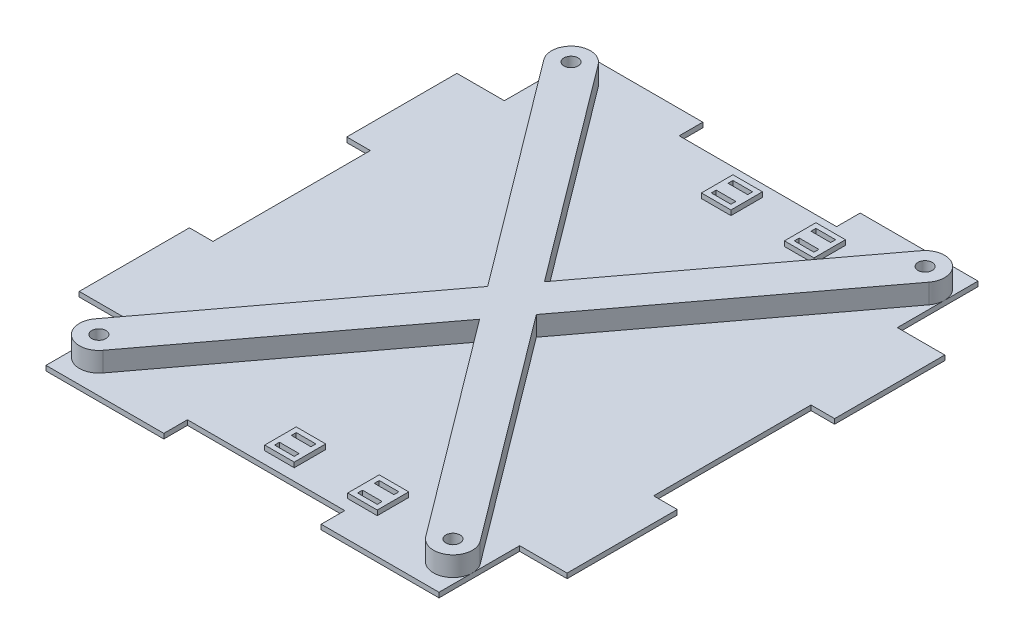
SolidWorks part; units mm, degrees
ref_plane "Front Plane" through (0, 0, 0) normal (0, 0, 1) x (1, 0, 0)
ref_plane "Top Plane" through (0, 0, 0) normal (0, 1, 0) x (1, 0, 0)
ref_plane "Right Plane" through (0, 0, 0) normal (1, 0, 0) x (0, 0, -1)
sketch "Sketch1" plane through (0, 0, 0) normal (0, 1, 0) x (1, 0, 0)
  line L0 (-25.4, 86.995) -> (-63.4314, 86.995)
  line L1 (-88.9, -101.6) -> (88.9, -101.6) construction
  line L2 (101.6, -88.9) -> (101.6, 88.9) construction
  line L3 (88.9, 101.6) -> (-88.9, 101.6) construction
  line L4 (-78.74, -60.96) -> (-63.4314, -60.96)
  line L5 (-63.4314, -60.96) -> (-63.4314, -86.995)
  line L6 (-63.4314, -86.995) -> (-25.4, -86.995)
  line L7 (63.4314, -86.995) -> (63.4314, -60.96)
  line L8 (63.4314, -60.96) -> (78.74, -60.96)
  line L9 (78.74, -60.96) -> (78.74, -25.4)
  line L10 (78.74, 60.96) -> (63.4314, 60.96)
  line L11 (63.4314, 60.96) -> (63.4314, 86.995)
  line L12 (63.4314, 86.995) -> (25.4, 86.995)
  line L13 (-63.4314, 86.995) -> (-63.4314, 60.96)
  line L14 (-63.4314, 60.96) -> (-78.74, 60.96)
  line L15 (-78.74, 60.96) -> (-78.74, 25.4)
  line L16 (-78.74, -25.4) -> (-78.74, -60.96)
  line L17 (-78.74, -25.4) -> (-71.12, -25.4)
  line L19 (-78.74, 25.4) -> (-71.12, 25.4)
  line L20 (-71.12, -25.4) -> (-71.12, 25.4)
  line L22 (-25.4, 86.995) -> (-25.4, 79.375)
  line L23 (-25.4, 79.375) -> (25.4, 79.375)
  line L24 (25.4, 86.995) -> (25.4, 79.375)
  line L25 (78.74, 25.4) -> (71.12, 25.4)
  line L27 (78.74, -25.4) -> (71.12, -25.4)
  line L28 (71.12, 25.4) -> (71.12, -25.4)
  line L30 (25.4, -86.995) -> (25.4, -79.375)
  line L31 (25.4, -79.375) -> (-25.4, -79.375)
  line L32 (-25.4, -86.995) -> (-25.4, -79.375)
  line L33 (78.74, 25.4) -> (78.74, 60.96)
  line L34 (25.4, -86.995) -> (63.4314, -86.995)
  line L35 (-101.6, 88.9) -> (-101.6, -88.9) construction
  arc A0 (88.9, -101.6) -> (101.6, -88.9) centre (88.9, -88.9) ccw construction
  arc A1 (-101.6, -88.9) -> (-88.9, -101.6) centre (-88.9, -88.9) ccw construction
  arc A2 (101.6, 88.9) -> (88.9, 101.6) centre (88.9, 88.9) ccw construction
  arc A3 (-101.6, 88.9) -> (-88.9, 101.6) centre (-88.9, 88.9) cw construction
  circle A4 centre (-57.15, 76.2) radius 2.286
  circle A5 centre (57.15, 76.2) radius 2.286
  circle A6 centre (57.15, -76.2) radius 2.286
  circle A7 centre (-57.15, -76.2) radius 2.286
  point P3 (0, 101.6)
  point P5 (101.6, 0)
  point P13 (101.6, 101.6)
  point P16 (-101.6, 101.6)
  point P38 (-71.12, 0)
  point P55 (0, -79.375)
  point P56 (0, 79.375)
  point P57 (71.12, 0)
  dimension "D2" = 12.7
  dimension "D11" = 4.572
  dimension "D8" = 44.45
  dimension "D1" = 203.2
  dimension "D3" = 203.2
  dimension "D4" = 22.86
  dimension "D5" = 15.3086
  dimension "D6" = 35.56
  dimension "D7" = 173.99
  dimension "D12" = 50.8
  dimension "D13" = 25.4
  dimension "D14" = 44.45
  dimension "D15" = 25.4
  dimension "D18" = 7.62
extrude "Main Body" add sketch "Sketch1" along normal blind 1.5875
sketch "Sketch3" plane through (0, 1.5875, 0) normal (0, 1, 0) x (1, 0, 0)
  line L0 (-57.15, -76.2) -> (57.15, 76.2) construction
  line L1 (52.1249, -79.9689) -> (62.1751, -72.4311)
  line L2 (-62.1751, 72.4311) -> (-52.1249, 79.9689)
  line L3 (62.1751, 72.4311) -> (52.1249, 79.9689)
  line L4 (-52.1249, -79.9689) -> (-62.1751, -72.4311)
  line L5 (-57.15, 76.2) -> (57.15, -76.2) construction
  line L6 (52.1249, 79.9689) -> (-62.1751, -72.4311)
  line L7 (-52.1249, -79.9689) -> (62.1751, 72.4311)
  line L8 (-52.1249, 79.9689) -> (62.1751, -72.4311)
  line L9 (52.1249, -79.9689) -> (-62.1751, 72.4311)
  line L28 (-78.74, -25.4) -> (-78.74, -60.96)
  line L29 (-78.74, -60.96) -> (-63.4314, -60.96)
  line L30 (-63.4314, -60.96) -> (-63.4314, -86.995)
  line L31 (-63.4314, -86.995) -> (-25.4, -86.995)
  line L32 (-25.4, -86.995) -> (-25.4, -79.375)
  line L33 (-25.4, -79.375) -> (25.4, -79.375)
  line L34 (25.4, -79.375) -> (25.4, -86.995)
  line L35 (25.4, -86.995) -> (63.4314, -86.995)
  line L36 (63.4314, -86.995) -> (63.4314, -60.96)
  line L37 (63.4314, -60.96) -> (78.74, -60.96)
  line L38 (78.74, -60.96) -> (78.74, -25.4)
  line L39 (78.74, -25.4) -> (71.12, -25.4)
  line L40 (71.12, -25.4) -> (71.12, 25.4)
  line L41 (71.12, 25.4) -> (78.74, 25.4)
  line L42 (78.74, 25.4) -> (78.74, 60.96)
  line L43 (78.74, 60.96) -> (63.4314, 60.96)
  line L44 (63.4314, 60.96) -> (63.4314, 86.995)
  line L45 (63.4314, 86.995) -> (25.4, 86.995)
  line L46 (25.4, 86.995) -> (25.4, 79.375)
  line L47 (25.4, 79.375) -> (-25.4, 79.375)
  line L48 (-25.4, 79.375) -> (-25.4, 86.995)
  line L49 (-25.4, 86.995) -> (-63.4314, 86.995)
  line L50 (-63.4314, 86.995) -> (-63.4314, 60.96)
  line L51 (-63.4314, 60.96) -> (-78.74, 60.96)
  line L52 (-78.74, 60.96) -> (-78.74, 25.4)
  line L53 (-78.74, 25.4) -> (-71.12, 25.4)
  line L54 (-71.12, 25.4) -> (-71.12, -25.4)
  line L55 (-71.12, -25.4) -> (-78.74, -25.4)
  line L56 (-78.74, -25.4) -> (-78.74, -60.96)
  line L57 (-78.74, -60.96) -> (-63.4314, -60.96)
  line L58 (-63.4314, -60.96) -> (-63.4314, -86.995)
  line L59 (-63.4314, -86.995) -> (-25.4, -86.995)
  line L60 (-25.4, -86.995) -> (-25.4, -79.375)
  line L61 (-25.4, -79.375) -> (25.4, -79.375)
  line L62 (25.4, -79.375) -> (25.4, -86.995)
  line L63 (25.4, -86.995) -> (63.4314, -86.995)
  line L64 (63.4314, -86.995) -> (63.4314, -60.96)
  line L65 (63.4314, -60.96) -> (78.74, -60.96)
  line L66 (78.74, -60.96) -> (78.74, -25.4)
  line L67 (78.74, -25.4) -> (71.12, -25.4)
  line L68 (71.12, -25.4) -> (71.12, 25.4)
  line L69 (71.12, 25.4) -> (78.74, 25.4)
  line L70 (78.74, 25.4) -> (78.74, 60.96)
  line L71 (78.74, 60.96) -> (63.4314, 60.96)
  line L72 (63.4314, 60.96) -> (63.4314, 86.995)
  line L73 (63.4314, 86.995) -> (25.4, 86.995)
  line L74 (25.4, 86.995) -> (25.4, 79.375)
  line L75 (25.4, 79.375) -> (-25.4, 79.375)
  line L76 (-25.4, 79.375) -> (-25.4, 86.995)
  line L77 (-25.4, 86.995) -> (-63.4314, 86.995)
  line L78 (-63.4314, 86.995) -> (-63.4314, 60.96)
  line L79 (-63.4314, 60.96) -> (-78.74, 60.96)
  line L80 (-78.74, 60.96) -> (-78.74, 25.4)
  line L81 (-78.74, 25.4) -> (-71.12, 25.4)
  line L82 (-71.12, 25.4) -> (-71.12, -25.4)
  line L83 (-71.12, -25.4) -> (-78.74, -25.4)
  circle A0 centre (-57.15, -76.2) radius 2.286 construction
  circle A1 centre (57.15, -76.2) radius 2.286 construction
  circle A2 centre (57.15, 76.2) radius 2.286 construction
  circle A3 centre (-57.15, 76.2) radius 2.286 construction
  circle A4 centre (-57.15, -76.2) radius 2.286
  circle A5 centre (57.15, -76.2) radius 2.286
  circle A6 centre (57.15, 76.2) radius 2.286
  circle A7 centre (-57.15, 76.2) radius 2.286
  circle A8 centre (-57.15, 76.2) radius 6.2814
  circle A9 centre (57.15, 76.2) radius 6.2814
  circle A10 centre (-57.15, -76.2) radius 6.2814
  circle A11 centre (57.15, -76.2) radius 6.2814
  point P42 (-57.15, 76.2)
  point P48 (57.15, 76.2)
  point P54 (-57.15, -76.2)
  point P56 (57.15, -76.2)
  circle M44 centre (57.15, -76.2) radius 2.286
  circle M45 centre (-57.15, 76.2) radius 2.286
  circle M74 centre (57.15, 76.2) radius 2.286
  circle M75 centre (-57.15, -76.2) radius 2.286
  dimension "D2" = 90
  dimension "D3" = 90
  dimension "D4" = 90
  dimension "D5" = 90
  dimension "D1" = 0
extrude "Boss-Extrude1" add sketch "Sketch3" along normal blind 6.35 contours A8 L9 L6 L8 | A9 L6 L8 L7 | L9 L7 L8 L6 | A10 L7 L9 L6 | A11 L8 L7 L9 | L2 A8 M45 | L2 A8 M45 | L3 A9 M74 | L3 A9 M74 | L1 A11 M44 | A11 L1 M44 | L4 A10 M75 | L4 A10 M75 | A7
sketch "Sketch2" plane through (0, 1.5875, 0) normal (0, 1, 0) x (1, 0, 0)
  line L0 (0, 0) -> (15.1112, 0) construction
  line L1 (-50.8, -63.5) -> (50.8, -63.5)
  line L2 (-50.8, -63.5) -> (-50.8, 63.5)
  line L3 (-50.8, 63.5) -> (50.8, 63.5)
  line L4 (50.8, -63.5) -> (50.8, 63.5)
  line L5 (-50.8, -63.5) -> (50.8, 63.5) construction
  line L6 (-50.8, 63.5) -> (50.8, -63.5) construction
  line L7 (-5.842, 63.5) -> (30.48, 63.5)
  line L8 (-5.842, 63.5) -> (-5.842, 68.58)
  line L9 (-5.842, 68.58) -> (30.48, 68.58)
  line L10 (30.48, 63.5) -> (30.48, 68.58)
  line L11 (-5.842, -63.5) -> (30.48, -63.5)
  line L12 (-5.842, -63.5) -> (-5.842, -68.58)
  line L13 (-5.842, -68.58) -> (30.48, -68.58)
  line L14 (30.48, -63.5) -> (30.48, -68.58)
  line L15 (-5.842, 68.58) -> (30.48, 68.58)
  line L16 (-5.842, 68.58) -> (-5.842, 72.39)
  line L17 (-5.842, 72.39) -> (30.48, 72.39)
  line L18 (30.48, 68.58) -> (30.48, 72.39)
  line L19 (-5.842, -68.58) -> (30.48, -68.58)
  line L20 (-5.842, -68.58) -> (-5.842, -72.39)
  line L21 (-5.842, -72.39) -> (30.48, -72.39)
  line L22 (30.48, -68.58) -> (30.48, -72.39)
  line L28 (62.1751, 72.4311) -> (7.8518, 0)
  line L29 (62.1751, 72.4311) -> (7.8518, 0)
  line L30 (7.8518, 0) -> (62.1751, -72.4311)
  line L31 (7.8518, 0) -> (62.1751, -72.4311)
  line L32 (63.4314, -76.2) -> (63.4314, -60.96)
  line L33 (63.4314, -76.2) -> (63.4314, -60.96)
  line L34 (30.48, -73.9775) -> (24.13, -73.9775)
  line L35 (-2.667, 72.39) -> (3.683, 72.39)
  line L36 (-2.667, 72.39) -> (-2.667, 73.9775)
  line L37 (63.4314, -60.96) -> (78.74, -60.96)
  line L38 (78.74, -60.96) -> (78.74, -25.4)
  line L39 (78.74, -25.4) -> (71.12, -25.4)
  line L40 (71.12, -25.4) -> (71.12, 25.4)
  line L41 (71.12, 25.4) -> (78.74, 25.4)
  line L42 (78.74, 25.4) -> (78.74, 60.96)
  line L43 (78.74, 60.96) -> (63.4314, 60.96)
  line L44 (63.4314, 60.96) -> (63.4314, 76.2)
  line L45 (-2.667, 73.9775) -> (3.683, 73.9775)
  line L46 (3.683, 72.39) -> (3.683, 73.9775)
  line L47 (-2.667, 68.58) -> (3.683, 68.58)
  line L48 (-2.667, 68.58) -> (-2.667, 66.9925)
  line L49 (-2.667, 66.9925) -> (3.683, 66.9925)
  line L50 (3.683, 68.58) -> (3.683, 66.9925)
  line L51 (30.48, 72.39) -> (24.13, 72.39)
  line L52 (30.48, 72.39) -> (30.48, 73.9775)
  line L53 (30.48, 73.9775) -> (24.13, 73.9775)
  line L54 (24.13, 72.39) -> (24.13, 73.9775)
  line L55 (30.48, 68.58) -> (24.13, 68.58)
  line L65 (63.4314, -60.96) -> (78.74, -60.96)
  line L66 (78.74, -60.96) -> (78.74, -25.4)
  line L67 (78.74, -25.4) -> (71.12, -25.4)
  line L68 (71.12, -25.4) -> (71.12, 25.4)
  line L69 (71.12, 25.4) -> (78.74, 25.4)
  line L70 (78.74, 25.4) -> (78.74, 60.96)
  line L71 (78.74, 60.96) -> (63.4314, 60.96)
  line L72 (63.4314, 60.96) -> (63.4314, 76.2)
  line L95 (30.48, 68.58) -> (30.48, 66.9925)
  line L96 (30.48, 66.9925) -> (24.13, 66.9925)
  line L97 (24.13, 68.58) -> (24.13, 66.9925)
  line L98 (24.13, -72.39) -> (24.13, -73.9775)
  line L99 (30.48, -72.39) -> (24.13, -72.39)
  line L100 (30.48, -72.39) -> (30.48, -73.9775)
  line L101 (30.48, -66.9925) -> (24.13, -66.9925)
  line L102 (24.13, -68.58) -> (24.13, -66.9925)
  line L103 (30.48, -68.58) -> (24.13, -68.58)
  line L104 (30.48, -68.58) -> (30.48, -66.9925)
  line L105 (-2.667, -66.9925) -> (3.683, -66.9925)
  line L106 (3.683, -68.58) -> (3.683, -66.9925)
  line L107 (-2.667, -68.58) -> (3.683, -68.58)
  line L108 (-2.667, -68.58) -> (-2.667, -66.9925)
  line L109 (-2.667, -73.9775) -> (3.683, -73.9775)
  line L110 (3.683, -72.39) -> (3.683, -73.9775)
  line L111 (-2.667, -72.39) -> (3.683, -72.39)
  line L112 (-2.667, -72.39) -> (-2.667, -73.9775)
  arc A2 (62.1751, 72.4311) -> (63.4314, 76.2) centre (57.15, 76.2) ccw
  arc A3 (62.1751, 72.4311) -> (63.4314, 76.2) centre (57.15, 76.2) ccw
  arc A4 (63.4314, -76.2) -> (62.1751, -72.4311) centre (57.15, -76.2) ccw
  arc A5 (63.4314, -76.2) -> (62.1751, -72.4311) centre (57.15, -76.2) ccw
  point P2 (0, 0)
  dimension "D2" = 101.6
  dimension "D3" = 127
  dimension "D4" = 36.322
  dimension "D5" = 20.32
  dimension "D6" = 5.08
  dimension "D7" = 3.81
  dimension "D8" = 6.35
  dimension "D9" = 3.175
  dimension "D10" = 1.5875
  dimension "D1" = 0
extrude "Cut-Extrude2" cut sketch "Sketch2" against normal up to next contours L108 L19 L106 L105 | L21 L112 L109 L110 | L102 L19 L14 L101 | L100 L21 L98 L34 | L50 L15 L48 L49 | L17 L46 L45 L36 | L54 L17 L52 L53 | L15 L97 L96 L10
sketch "Sketch5" plane through (0, 1.5875, 0) normal (0, 1, 0) x (1, 0, 0)
  line L0 (-4.2545, 70.8025) -> (-4.2545, 70.1675)
  line L1 (5.2705, 70.8025) -> (5.2705, 70.1675)
  line L2 (22.5425, 70.8025) -> (22.5425, 70.1675)
  line L3 (32.0675, 70.8025) -> (32.0675, 70.1675)
  line L4 (24.13, -68.58) -> (30.48, -68.58)
  line L5 (30.48, -66.9925) -> (30.48, -68.58)
  line L6 (30.48, -66.9925) -> (24.13, -66.9925)
  line L7 (24.13, -68.58) -> (24.13, -66.9925)
  line L8 (24.13, -72.39) -> (30.48, -72.39)
  line L9 (24.13, 68.58) -> (24.13, 66.9925) construction
  line L10 (30.48, 66.9925) -> (24.13, 66.9925) construction
  line L11 (30.48, 66.9925) -> (30.48, 68.58) construction
  line L12 (24.13, 68.58) -> (30.48, 68.58) construction
  line L13 (30.48, 72.39) -> (30.48, 73.9775) construction
  line L14 (24.13, 72.39) -> (30.48, 72.39) construction
  line L15 (30.48, 73.9775) -> (24.13, 73.9775) construction
  line L16 (24.13, 72.39) -> (24.13, 73.9775) construction
  line L17 (3.683, 68.58) -> (3.683, 66.9925) construction
  line L18 (0, 10.469) -> (52.1249, 79.9689)
  line L19 (63.4314, 76.2) -> (63.4314, 86.995)
  line L20 (63.4314, 86.995) -> (25.4, 86.995)
  line L21 (25.4, 86.995) -> (25.4, 79.375)
  line L22 (25.4, 79.375) -> (-25.4, 79.375)
  line L23 (-25.4, 79.375) -> (-25.4, 86.995)
  line L24 (-25.4, 86.995) -> (-63.4314, 86.995)
  line L25 (-63.4314, 86.995) -> (-63.4314, 76.2)
  line L26 (-52.1249, 79.9689) -> (0, 10.469)
  line L27 (0, 10.469) -> (52.1249, 79.9689)
  line L28 (63.4314, 76.2) -> (63.4314, 86.995)
  line L29 (63.4314, 86.995) -> (25.4, 86.995)
  line L30 (25.4, 86.995) -> (25.4, 79.375)
  line L31 (25.4, 79.375) -> (-25.4, 79.375)
  line L32 (-25.4, 79.375) -> (-25.4, 86.995)
  line L33 (-25.4, 86.995) -> (-63.4314, 86.995)
  line L34 (-63.4314, 86.995) -> (-63.4314, 76.2)
  line L35 (-52.1249, 79.9689) -> (0, 10.469)
  line L36 (-2.667, 66.9925) -> (3.683, 66.9925) construction
  line L37 (-2.667, 68.58) -> (-2.667, 66.9925) construction
  line L38 (-2.667, 68.58) -> (3.683, 68.58) construction
  line L39 (3.683, 72.39) -> (3.683, 73.9775) construction
  line L40 (-2.667, 72.39) -> (3.683, 72.39) construction
  line L41 (-2.667, 72.39) -> (-2.667, 73.9775) construction
  line L42 (-2.667, 73.9775) -> (3.683, 73.9775) construction
  line L43 (24.13, 68.58) -> (24.13, 66.9925)
  line L44 (30.48, 66.9925) -> (24.13, 66.9925)
  line L45 (30.48, 66.9925) -> (30.48, 68.58)
  line L46 (24.13, 68.58) -> (30.48, 68.58)
  line L47 (30.48, 72.39) -> (30.48, 73.9775)
  line L48 (24.13, 72.39) -> (30.48, 72.39)
  line L49 (30.48, 73.9775) -> (24.13, 73.9775)
  line L50 (24.13, 72.39) -> (24.13, 73.9775)
  line L51 (3.683, 68.58) -> (3.683, 66.9925)
  line L52 (-2.667, 66.9925) -> (3.683, 66.9925)
  line L53 (-2.667, 68.58) -> (-2.667, 66.9925)
  line L54 (-2.667, 68.58) -> (3.683, 68.58)
  line L55 (3.683, 72.39) -> (3.683, 73.9775)
  line L56 (-2.667, 72.39) -> (3.683, 72.39)
  line L57 (-2.667, 72.39) -> (-2.667, 73.9775)
  line L58 (-2.667, 73.9775) -> (3.683, 73.9775)
  line L59 (0, 0) -> (19.0271, 0) construction
  line L61 (-4.2545, 70.8025) -> (-4.2545, 75.565)
  line L62 (-4.2545, 75.565) -> (5.2705, 75.565)
  line L63 (5.2705, 70.8025) -> (5.2705, 75.565)
  line L64 (-4.2545, 70.8025) -> (5.2705, 75.565) construction
  line L65 (-4.2545, 75.565) -> (5.2705, 70.8025) construction
  line L66 (-4.2545, 65.405) -> (5.2705, 65.405)
  line L67 (-4.2545, 65.405) -> (-4.2545, 70.1675)
  line L69 (5.2705, 65.405) -> (5.2705, 70.1675)
  line L70 (-4.2545, 65.405) -> (5.2705, 70.1675) construction
  line L71 (-4.2545, 70.1675) -> (5.2705, 65.405) construction
  line L73 (22.5425, 70.8025) -> (22.5425, 75.565)
  line L74 (22.5425, 75.565) -> (32.0675, 75.565)
  line L75 (32.0675, 70.8025) -> (32.0675, 75.565)
  line L76 (22.5425, 70.8025) -> (32.0675, 75.565) construction
  line L77 (22.5425, 75.565) -> (32.0675, 70.8025) construction
  line L78 (22.5425, 65.405) -> (32.0675, 65.405)
  line L79 (22.5425, 65.405) -> (22.5425, 70.1675)
  line L81 (32.0675, 65.405) -> (32.0675, 70.1675)
  line L82 (22.5425, 65.405) -> (32.0675, 70.1675) construction
  line L83 (22.5425, 70.1675) -> (32.0675, 65.405) construction
  line L84 (24.13, -72.39) -> (24.13, -73.9775)
  line L85 (30.48, -73.9775) -> (24.13, -73.9775)
  line L86 (30.48, -72.39) -> (30.48, -73.9775)
  line L87 (22.5425, -70.8025) -> (22.5425, -75.565)
  line L88 (22.5425, -75.565) -> (32.0675, -75.565)
  line L89 (32.0675, -70.8025) -> (32.0675, -75.565)
  line L90 (32.0675, -70.8025) -> (32.0675, -70.1675)
  line L91 (32.0675, -65.405) -> (32.0675, -70.1675)
  line L92 (22.5425, -65.405) -> (32.0675, -65.405)
  line L93 (22.5425, -65.405) -> (22.5425, -70.1675)
  line L94 (22.5425, -70.8025) -> (22.5425, -70.1675)
  line L95 (-2.667, -68.58) -> (3.683, -68.58)
  line L96 (-2.667, -68.58) -> (-2.667, -66.9925)
  line L97 (-2.667, -66.9925) -> (3.683, -66.9925)
  line L98 (3.683, -68.58) -> (3.683, -66.9925)
  line L99 (-2.667, -72.39) -> (3.683, -72.39)
  line L100 (-2.667, -72.39) -> (-2.667, -73.9775)
  line L101 (-2.667, -73.9775) -> (3.683, -73.9775)
  line L102 (3.683, -72.39) -> (3.683, -73.9775)
  line L103 (-4.2545, -70.8025) -> (-4.2545, -75.565)
  line L104 (-4.2545, -75.565) -> (5.2705, -75.565)
  line L105 (5.2705, -70.8025) -> (5.2705, -75.565)
  line L106 (5.2705, -70.8025) -> (5.2705, -70.1675)
  line L107 (5.2705, -65.405) -> (5.2705, -70.1675)
  line L108 (-4.2545, -65.405) -> (5.2705, -65.405)
  line L109 (-4.2545, -65.405) -> (-4.2545, -70.1675)
  line L110 (-4.2545, -70.8025) -> (-4.2545, -70.1675)
  arc A4 (63.4314, 76.2) -> (52.1249, 79.9689) centre (57.15, 76.2) ccw
  arc A5 (-52.1249, 79.9689) -> (-63.4314, 76.2) centre (-57.15, 76.2) ccw
  arc A6 (63.4314, 76.2) -> (52.1249, 79.9689) centre (57.15, 76.2) ccw
  arc A7 (-52.1249, 79.9689) -> (-63.4314, 76.2) centre (-57.15, 76.2) ccw
  point P7 (0.508, 73.9775)
  point P9 (-2.667, 73.1838)
  point P17 (0.508, 73.1838)
  point P19 (-2.667, 67.7863)
  point P24 (0.508, 67.7863)
  point P25 (27.305, 73.9775)
  point P27 (27.305, 73.1838)
  point P28 (27.305, 67.7863)
  point P32 (0.508, 67.7863)
  point P40 (0.508, 73.1838)
  point P47 (27.305, 67.7863)
  point P52 (27.305, 73.1838)
  line M41 (3.683, 72.39) -> (-2.667, 72.39)
  line M42 (-2.667, 72.39) -> (-2.667, 73.9775)
  line M43 (-2.667, 73.9775) -> (3.683, 73.9775)
  line M44 (3.683, 73.9775) -> (3.683, 72.39)
  line M56 (24.13, 66.9925) -> (24.13, 68.58)
  line M57 (24.13, 68.58) -> (30.48, 68.58)
  line M58 (30.48, 68.58) -> (30.48, 66.9925)
  line M59 (30.48, 66.9925) -> (24.13, 66.9925)
  line M60 (30.48, 72.39) -> (24.13, 72.39)
  line M61 (24.13, 72.39) -> (24.13, 73.9775)
  line M62 (24.13, 73.9775) -> (30.48, 73.9775)
  line M63 (30.48, 73.9775) -> (30.48, 72.39)
  line M64 (-2.667, 68.58) -> (3.683, 68.58)
  line M65 (3.683, 68.58) -> (3.683, 66.9925)
  line M66 (3.683, 66.9925) -> (-2.667, 66.9925)
  line M67 (-2.667, 66.9925) -> (-2.667, 68.58)
  dimension "D2" = 1.5875
  dimension "D3" = 1.5875
  dimension "D1" = 0
extrude "Boss-Extrude3" add sketch "Sketch5" along normal blind 1.5875 contours L110 L103 L104 L105 L106 L107 L108 L109 L98 L95 L96 L97 L99 L102 L101 L100 | L94 L87 L88 L89 L90 L91 L92 L93 L4 L7 L6 L5 L8 L86 L85 L84 | L66 L69 L1 L63 L62 L61 L0 L67 M44 M41 M42 M43 M67 M64 M65 M66 | L78 L81 L3 L75 L74 L73 L2 L79 M63 M60 M61 M62 M59 M56 M57 M58
